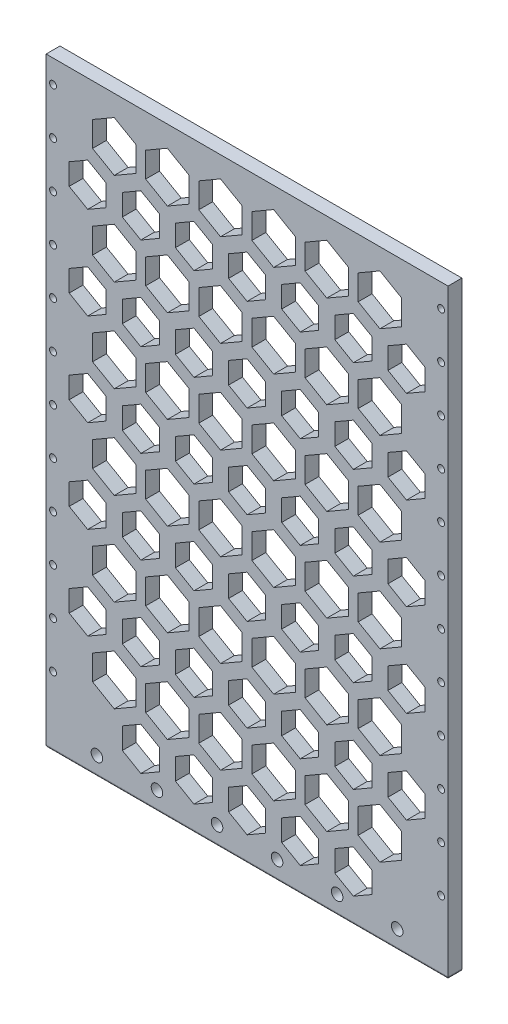
SolidWorks part; units mm, degrees
material "6061 Alloy"
ref_plane "前视基准面" through (0, 0, 0) normal (0, 0, 1) x (1, 0, 0)
ref_plane "上视基准面" through (0, 0, 0) normal (0, 1, 0) x (1, 0, 0)
ref_plane "右视基准面" through (0, 0, 0) normal (1, 0, 0) x (0, 0, -1)
sketch "Sketch1" plane through (0, 0, 0) normal (0, 0, 1) x (1, 0, 0)
  line L1 (-87, 90) -> (87, 90)
  line L2 (-87, 90) -> (-87, -150)
  line L3 (-87, -150) -> (87, -150)
  line L4 (87, 90) -> (87, -150)
  line L5 (-87, 90) -> (87, -150) construction
  line L6 (-87, -150) -> (87, 90) construction
  point P0 (0, -30)
  dimension "D1" = 174
  dimension "D2" = 240
extrude "Boss-Extrude1" add sketch "Sketch1" along normal blind 6
sketch "Sketch3" plane through (0, 0, 6) normal (0, 0, 1) x (1, 0, 0)
  line L6 (-77, -134) -> (77, -134) construction
  line L7 (-77, -134) -> (-77, -150) construction
  line L8 (-77, -150) -> (77, -150) construction
  line L9 (77, -134) -> (77, -150) construction
  line L10 (-77, -134) -> (77, -150) construction
  line L11 (-77, -150) -> (77, -134) construction
  circle A0 centre (-65, -142) radius 2.5
  circle A1 centre (-39, -142) radius 2.5
  circle A2 centre (-13, -142) radius 2.5
  circle A3 centre (13, -142) radius 2.5
  circle A4 centre (39, -142) radius 2.5
  circle A5 centre (65, -142) radius 2.5
  point P0 (0, -142)
  dimension "D1" = 12
  dimension "D2" = 6
extrude "Cut-Extrude1" cut sketch "Sketch3" against normal blind 6 contours A0 | A1 | A2 | A3 | A4 | A5
sketch "Sketch4" plane through (0, 90, 0) normal (0, 1, 0) x (1, 0, 0)
  line L4 (87, 0) -> (-87, 0)
  line L5 (-87, 0) -> (-87, -6)
  line L6 (-87, -6) -> (87, -6)
  line L7 (87, -6) -> (87, 0)
  line L8 (87, 0) -> (-87, 0)
  line L9 (-87, 0) -> (-87, -6)
  line L10 (-87, -6) -> (87, -6)
  line L11 (87, -6) -> (87, 0)
  dimension "D1" = 0
extrude "Boss-Extrude2" add sketch "Sketch4" along normal blind 20
sketch "Sketch6" plane through (0, 0, 6) normal (0, 0, 1) x (1, 0, 0)
  line L0 (-87, 110) -> (87, 110) construction
  line L2 (-87, 110) -> (-87, -150) construction
  line L3 (87, -150) -> (87, 110) construction
  circle A0 centre (-84, 100) radius 1.5
  circle A1 centre (-84, 80) radius 1.5
  circle A2 centre (-84, 60) radius 1.5
  circle A3 centre (-84, 40) radius 1.5
  circle A4 centre (-84, 20) radius 1.5
  circle A5 centre (-84, 0) radius 1.5
  circle A6 centre (-84, -20) radius 1.5
  circle A7 centre (-84, -40) radius 1.5
  circle A8 centre (-84, -60) radius 1.5
  circle A9 centre (-84, -80) radius 1.5
  circle A10 centre (-84, -100) radius 1.5
  circle A11 centre (-84, -120) radius 1.5
  circle A15 centre (84, 100) radius 1.5
  circle A16 centre (84, 80) radius 1.5
  circle A17 centre (84, 60) radius 1.5
  circle A18 centre (84, 40) radius 1.5
  circle A19 centre (84, 20) radius 1.5
  circle A20 centre (84, 0) radius 1.5
  circle A21 centre (84, -20) radius 1.5
  circle A22 centre (84, -40) radius 1.5
  circle A23 centre (84, -60) radius 1.5
  circle A24 centre (84, -80) radius 1.5
  circle A25 centre (84, -100) radius 1.5
  circle A26 centre (84, -120) radius 1.5
  circle A30 centre (-84, -160) radius 1.5 [skipped]
  circle A31 centre (-84, -180) radius 1.5 [skipped]
  circle A32 centre (84, -160) radius 1.5 [skipped]
  circle A33 centre (84, -180) radius 1.5 [skipped]
  circle A34 centre (-84, -140) radius 1.5 [skipped]
  circle A35 centre (84, -140) radius 1.5 [skipped]
  dimension "D3" = 15
  dimension "D5" = 3
  dimension "D1" = 10
  dimension "D2" = 3
  dimension "D4" = 3
  dimension "D6" = 10
  dimension "D7" = 15
extrude "Cut-Extrude2" cut sketch "Sketch6" against normal blind 10
sketch "Sketch7" plane through (0, 0, 6) normal (0, 0, 1) x (1, 0, 0)
  line L80 (-46, 60.7624) -> (-38, 65.3812)
  line L81 (-38, 65.3812) -> (-38, 74.6188)
  line L82 (-38, 74.6188) -> (-46, 79.2376)
  line L83 (-46, 79.2376) -> (-54, 74.6188)
  line L84 (-54, 74.6188) -> (-54, 65.3812)
  line L85 (-54, 65.3812) -> (-46, 60.7624)
  line L86 (-23, 60.7624) -> (-15, 65.3812)
  line L87 (-15, 65.3812) -> (-15, 74.6188)
  line L88 (-15, 74.6188) -> (-23, 79.2376)
  line L89 (-23, 79.2376) -> (-31, 74.6188)
  line L90 (-31, 74.6188) -> (-31, 65.3812)
  line L91 (-31, 65.3812) -> (-23, 60.7624)
  line L92 (0, 60.7624) -> (8, 65.3812)
  line L93 (8, 65.3812) -> (8, 74.6188)
  line L94 (8, 74.6188) -> (0, 79.2376)
  line L95 (0, 79.2376) -> (-8, 74.6188)
  line L96 (-8, 74.6188) -> (-8, 65.3812)
  line L97 (-8, 65.3812) -> (0, 60.7624)
  line L98 (23, 60.7624) -> (31, 65.3812)
  line L99 (31, 65.3812) -> (31, 74.6188)
  line L100 (31, 74.6188) -> (23, 79.2376)
  line L101 (23, 79.2376) -> (15, 74.6188)
  line L102 (15, 74.6188) -> (15, 65.3812)
  line L103 (15, 65.3812) -> (23, 60.7624)
  line L104 (46, 60.7624) -> (54, 65.3812)
  line L105 (54, 65.3812) -> (54, 74.6188)
  line L106 (54, 74.6188) -> (46, 79.2376)
  line L107 (46, 79.2376) -> (38, 74.6188)
  line L108 (38, 74.6188) -> (38, 65.3812)
  line L109 (38, 65.3812) -> (46, 60.7624)
  line L110 (69, 60.7624) -> (77, 65.3812)
  line L111 (77, 65.3812) -> (77, 74.6188)
  line L112 (77, 74.6188) -> (69, 79.2376)
  line L113 (69, 79.2376) -> (61, 74.6188)
  line L114 (61, 74.6188) -> (61, 65.3812)
  line L115 (61, 65.3812) -> (69, 60.7624)
  line L116 (-46, 20.7624) -> (-38, 25.3812)
  line L117 (-38, 25.3812) -> (-38, 34.6188)
  line L118 (-38, 34.6188) -> (-46, 39.2376)
  line L119 (-46, 39.2376) -> (-54, 34.6188)
  line L120 (-54, 34.6188) -> (-54, 25.3812)
  line L121 (-54, 25.3812) -> (-46, 20.7624)
  line L122 (-23, 20.7624) -> (-15, 25.3812)
  line L123 (-15, 25.3812) -> (-15, 34.6188)
  line L124 (-15, 34.6188) -> (-23, 39.2376)
  line L125 (-23, 39.2376) -> (-31, 34.6188)
  line L126 (-31, 34.6188) -> (-31, 25.3812)
  line L127 (-31, 25.3812) -> (-23, 20.7624)
  line L128 (0, 20.7624) -> (8, 25.3812)
  line L129 (8, 25.3812) -> (8, 34.6188)
  line L130 (8, 34.6188) -> (0, 39.2376)
  line L131 (0, 39.2376) -> (-8, 34.6188)
  line L132 (-8, 34.6188) -> (-8, 25.3812)
  line L133 (-8, 25.3812) -> (0, 20.7624)
  line L134 (23, 20.7624) -> (31, 25.3812)
  line L135 (31, 25.3812) -> (31, 34.6188)
  line L136 (31, 34.6188) -> (23, 39.2376)
  line L137 (23, 39.2376) -> (15, 34.6188)
  line L138 (15, 34.6188) -> (15, 25.3812)
  line L139 (15, 25.3812) -> (23, 20.7624)
  line L140 (46, 20.7624) -> (54, 25.3812)
  line L141 (54, 25.3812) -> (54, 34.6188)
  line L142 (54, 34.6188) -> (46, 39.2376)
  line L143 (46, 39.2376) -> (38, 34.6188)
  line L144 (38, 34.6188) -> (38, 25.3812)
  line L145 (38, 25.3812) -> (46, 20.7624)
  line L146 (69, 20.7624) -> (77, 25.3812)
  line L147 (77, 25.3812) -> (77, 34.6188)
  line L148 (77, 34.6188) -> (69, 39.2376)
  line L149 (69, 39.2376) -> (61, 34.6188)
  line L150 (61, 34.6188) -> (61, 25.3812)
  line L151 (61, 25.3812) -> (69, 20.7624)
  line L152 (-46, -19.2376) -> (-38, -14.6188)
  line L153 (-38, -14.6188) -> (-38, -5.3812)
  line L154 (-38, -5.3812) -> (-46, -0.7624)
  line L155 (-46, -0.7624) -> (-54, -5.3812)
  line L156 (-54, -5.3812) -> (-54, -14.6188)
  line L157 (-54, -14.6188) -> (-46, -19.2376)
  line L158 (-23, -19.2376) -> (-15, -14.6188)
  line L159 (-15, -14.6188) -> (-15, -5.3812)
  line L160 (-15, -5.3812) -> (-23, -0.7624)
  line L161 (-23, -0.7624) -> (-31, -5.3812)
  line L162 (-31, -5.3812) -> (-31, -14.6188)
  line L163 (-31, -14.6188) -> (-23, -19.2376)
  line L164 (0, -19.2376) -> (8, -14.6188)
  line L165 (8, -14.6188) -> (8, -5.3812)
  line L166 (8, -5.3812) -> (0, -0.7624)
  line L167 (0, -0.7624) -> (-8, -5.3812)
  line L168 (-8, -5.3812) -> (-8, -14.6188)
  line L169 (-8, -14.6188) -> (0, -19.2376)
  line L170 (23, -19.2376) -> (31, -14.6188)
  line L171 (31, -14.6188) -> (31, -5.3812)
  line L172 (31, -5.3812) -> (23, -0.7624)
  line L173 (23, -0.7624) -> (15, -5.3812)
  line L174 (15, -5.3812) -> (15, -14.6188)
  line L175 (15, -14.6188) -> (23, -19.2376)
  line L176 (46, -19.2376) -> (54, -14.6188)
  line L177 (54, -14.6188) -> (54, -5.3812)
  line L178 (54, -5.3812) -> (46, -0.7624)
  line L179 (46, -0.7624) -> (38, -5.3812)
  line L180 (38, -5.3812) -> (38, -14.6188)
  line L181 (38, -14.6188) -> (46, -19.2376)
  line L182 (69, -19.2376) -> (77, -14.6188)
  line L183 (77, -14.6188) -> (77, -5.3812)
  line L184 (77, -5.3812) -> (69, -0.7624)
  line L185 (69, -0.7624) -> (61, -5.3812)
  line L186 (61, -5.3812) -> (61, -14.6188)
  line L187 (61, -14.6188) -> (69, -19.2376)
  line L188 (-46, -59.2376) -> (-38, -54.6188)
  line L189 (-38, -54.6188) -> (-38, -45.3812)
  line L190 (-38, -45.3812) -> (-46, -40.7624)
  line L191 (-46, -40.7624) -> (-54, -45.3812)
  line L192 (-54, -45.3812) -> (-54, -54.6188)
  line L193 (-54, -54.6188) -> (-46, -59.2376)
  line L194 (-23, -59.2376) -> (-15, -54.6188)
  line L195 (-15, -54.6188) -> (-15, -45.3812)
  line L196 (-15, -45.3812) -> (-23, -40.7624)
  line L197 (-23, -40.7624) -> (-31, -45.3812)
  line L198 (-31, -45.3812) -> (-31, -54.6188)
  line L199 (-31, -54.6188) -> (-23, -59.2376)
  line L200 (0, -59.2376) -> (8, -54.6188)
  line L201 (8, -54.6188) -> (8, -45.3812)
  line L202 (8, -45.3812) -> (0, -40.7624)
  line L203 (0, -40.7624) -> (-8, -45.3812)
  line L204 (-8, -45.3812) -> (-8, -54.6188)
  line L205 (-8, -54.6188) -> (0, -59.2376)
  line L206 (23, -59.2376) -> (31, -54.6188)
  line L207 (31, -54.6188) -> (31, -45.3812)
  line L208 (31, -45.3812) -> (23, -40.7624)
  line L209 (23, -40.7624) -> (15, -45.3812)
  line L210 (15, -45.3812) -> (15, -54.6188)
  line L211 (15, -54.6188) -> (23, -59.2376)
  line L212 (46, -59.2376) -> (54, -54.6188)
  line L213 (54, -54.6188) -> (54, -45.3812)
  line L214 (54, -45.3812) -> (46, -40.7624)
  line L215 (46, -40.7624) -> (38, -45.3812)
  line L216 (38, -45.3812) -> (38, -54.6188)
  line L217 (38, -54.6188) -> (46, -59.2376)
  line L218 (69, -59.2376) -> (77, -54.6188)
  line L219 (77, -54.6188) -> (77, -45.3812)
  line L220 (77, -45.3812) -> (69, -40.7624)
  line L221 (69, -40.7624) -> (61, -45.3812)
  line L222 (61, -45.3812) -> (61, -54.6188)
  line L223 (61, -54.6188) -> (69, -59.2376)
  line L224 (-46, -99.2376) -> (-38, -94.6188)
  line L225 (-38, -94.6188) -> (-38, -85.3812)
  line L226 (-38, -85.3812) -> (-46, -80.7624)
  line L227 (-46, -80.7624) -> (-54, -85.3812)
  line L228 (-54, -85.3812) -> (-54, -94.6188)
  line L229 (-54, -94.6188) -> (-46, -99.2376)
  line L230 (-23, -99.2376) -> (-15, -94.6188)
  line L231 (-15, -94.6188) -> (-15, -85.3812)
  line L232 (-15, -85.3812) -> (-23, -80.7624)
  line L233 (-23, -80.7624) -> (-31, -85.3812)
  line L234 (-31, -85.3812) -> (-31, -94.6188)
  line L235 (-31, -94.6188) -> (-23, -99.2376)
  line L236 (0, -99.2376) -> (8, -94.6188)
  line L237 (8, -94.6188) -> (8, -85.3812)
  line L238 (8, -85.3812) -> (0, -80.7624)
  line L239 (0, -80.7624) -> (-8, -85.3812)
  line L240 (-8, -85.3812) -> (-8, -94.6188)
  line L241 (-8, -94.6188) -> (0, -99.2376)
  line L242 (23, -99.2376) -> (31, -94.6188)
  line L243 (31, -94.6188) -> (31, -85.3812)
  line L244 (31, -85.3812) -> (23, -80.7624)
  line L245 (23, -80.7624) -> (15, -85.3812)
  line L246 (15, -85.3812) -> (15, -94.6188)
  line L247 (15, -94.6188) -> (23, -99.2376)
  line L248 (46, -99.2376) -> (54, -94.6188)
  line L249 (54, -94.6188) -> (54, -85.3812)
  line L250 (54, -85.3812) -> (46, -80.7624)
  line L251 (46, -80.7624) -> (38, -85.3812)
  line L252 (38, -85.3812) -> (38, -94.6188)
  line L253 (38, -94.6188) -> (46, -99.2376)
  line L254 (69, -99.2376) -> (77, -94.6188)
  line L255 (77, -94.6188) -> (77, -85.3812)
  line L256 (77, -85.3812) -> (69, -80.7624)
  line L257 (69, -80.7624) -> (61, -85.3812)
  line L258 (61, -85.3812) -> (61, -94.6188)
  line L259 (61, -94.6188) -> (69, -99.2376)
  line L260 (-46, -139.2376) -> (-38, -134.6188)
  line L261 (-38, -134.6188) -> (-38, -125.3812)
  line L262 (-38, -125.3812) -> (-46, -120.7624)
  line L263 (-46, -120.7624) -> (-54, -125.3812)
  line L264 (-54, -125.3812) -> (-54, -134.6188)
  line L265 (-54, -134.6188) -> (-46, -139.2376)
  line L266 (-23, -139.2376) -> (-15, -134.6188)
  line L267 (-15, -134.6188) -> (-15, -125.3812)
  line L268 (-15, -125.3812) -> (-23, -120.7624)
  line L269 (-23, -120.7624) -> (-31, -125.3812)
  line L270 (-31, -125.3812) -> (-31, -134.6188)
  line L271 (-31, -134.6188) -> (-23, -139.2376)
  line L272 (0, -139.2376) -> (8, -134.6188)
  line L273 (8, -134.6188) -> (8, -125.3812)
  line L274 (8, -125.3812) -> (0, -120.7624)
  line L275 (0, -120.7624) -> (-8, -125.3812)
  line L276 (-8, -125.3812) -> (-8, -134.6188)
  line L277 (-8, -134.6188) -> (0, -139.2376)
  line L278 (23, -139.2376) -> (31, -134.6188)
  line L279 (31, -134.6188) -> (31, -125.3812)
  line L280 (31, -125.3812) -> (23, -120.7624)
  line L281 (23, -120.7624) -> (15, -125.3812)
  line L282 (15, -125.3812) -> (15, -134.6188)
  line L283 (15, -134.6188) -> (23, -139.2376)
  line L284 (46, -139.2376) -> (54, -134.6188)
  line L285 (54, -134.6188) -> (54, -125.3812)
  line L286 (54, -125.3812) -> (46, -120.7624)
  line L287 (46, -120.7624) -> (38, -125.3812)
  line L288 (38, -125.3812) -> (38, -134.6188)
  line L289 (38, -134.6188) -> (46, -139.2376)
  line L302 (-69, 60.7624) -> (-61, 65.3812)
  line L303 (-61, 65.3812) -> (-61, 74.6188)
  line L304 (-61, 74.6188) -> (-69, 79.2376)
  line L305 (-69, 79.2376) -> (-77, 74.6188)
  line L306 (-77, 74.6188) -> (-77, 65.3812)
  line L307 (-77, 65.3812) -> (-69, 60.7624)
  line L308 (-69, 20.7624) -> (-61, 25.3812)
  line L309 (-61, 25.3812) -> (-61, 34.6188)
  line L310 (-61, 34.6188) -> (-69, 39.2376)
  line L311 (-69, 39.2376) -> (-77, 34.6188)
  line L312 (-77, 34.6188) -> (-77, 25.3812)
  line L313 (-77, 25.3812) -> (-69, 20.7624)
  line L314 (-69, -19.2376) -> (-61, -14.6188)
  line L315 (-61, -14.6188) -> (-61, -5.3812)
  line L316 (-61, -5.3812) -> (-69, -0.7624)
  line L317 (-69, -0.7624) -> (-77, -5.3812)
  line L318 (-77, -5.3812) -> (-77, -14.6188)
  line L319 (-77, -14.6188) -> (-69, -19.2376)
  line L320 (-69, -59.2376) -> (-61, -54.6188)
  line L321 (-61, -54.6188) -> (-61, -45.3812)
  line L322 (-61, -45.3812) -> (-69, -40.7624)
  line L323 (-69, -40.7624) -> (-77, -45.3812)
  line L324 (-77, -45.3812) -> (-77, -54.6188)
  line L325 (-77, -54.6188) -> (-69, -59.2376)
  line L326 (-69, -99.2376) -> (-61, -94.6188)
  line L327 (-61, -94.6188) -> (-61, -85.3812)
  line L328 (-61, -85.3812) -> (-69, -80.7624)
  line L329 (-69, -80.7624) -> (-77, -85.3812)
  line L330 (-77, -85.3812) -> (-77, -94.6188)
  line L331 (-77, -94.6188) -> (-69, -99.2376)
  line L376 (-34.5, 79.2376) -> (-25.109, 84.6595)
  line L377 (-25.109, 84.6595) -> (-25.109, 95.5033)
  line L378 (-25.109, 95.5033) -> (-34.5, 100.9252)
  line L379 (-34.5, 100.9252) -> (-43.891, 95.5033)
  line L380 (-43.891, 95.5033) -> (-43.891, 84.6595)
  line L381 (-43.891, 84.6595) -> (-34.5, 79.2376)
  line L382 (-11.5, 79.2376) -> (-2.109, 84.6595)
  line L383 (-2.109, 84.6595) -> (-2.109, 95.5033)
  line L384 (-2.109, 95.5033) -> (-11.5, 100.9252)
  line L385 (-11.5, 100.9252) -> (-20.891, 95.5033)
  line L386 (-20.891, 95.5033) -> (-20.891, 84.6595)
  line L387 (-20.891, 84.6595) -> (-11.5, 79.2376)
  line L388 (11.5, 79.2376) -> (20.891, 84.6595)
  line L389 (20.891, 84.6595) -> (20.891, 95.5033)
  line L390 (20.891, 95.5033) -> (11.5, 100.9252)
  line L391 (11.5, 100.9252) -> (2.109, 95.5033)
  line L392 (2.109, 95.5033) -> (2.109, 84.6595)
  line L393 (2.109, 84.6595) -> (11.5, 79.2376)
  line L394 (34.5, 79.2376) -> (43.891, 84.6595)
  line L395 (43.891, 84.6595) -> (43.891, 95.5033)
  line L396 (43.891, 95.5033) -> (34.5, 100.9252)
  line L397 (34.5, 100.9252) -> (25.109, 95.5033)
  line L398 (25.109, 95.5033) -> (25.109, 84.6595)
  line L399 (25.109, 84.6595) -> (34.5, 79.2376)
  line L400 (57.5, 79.2376) -> (66.891, 84.6595)
  line L401 (66.891, 84.6595) -> (66.891, 95.5033)
  line L402 (66.891, 95.5033) -> (57.5, 100.9252)
  line L403 (57.5, 100.9252) -> (48.109, 95.5033)
  line L404 (48.109, 95.5033) -> (48.109, 84.6595)
  line L405 (48.109, 84.6595) -> (57.5, 79.2376)
  line L406 (-34.5, 39.2376) -> (-25.109, 44.6595)
  line L407 (-25.109, 44.6595) -> (-25.109, 55.5033)
  line L408 (-25.109, 55.5033) -> (-34.5, 60.9252)
  line L409 (-34.5, 60.9252) -> (-43.891, 55.5033)
  line L410 (-43.891, 55.5033) -> (-43.891, 44.6595)
  line L411 (-43.891, 44.6595) -> (-34.5, 39.2376)
  line L412 (-11.5, 39.2376) -> (-2.109, 44.6595)
  line L413 (-2.109, 44.6595) -> (-2.109, 55.5033)
  line L414 (-2.109, 55.5033) -> (-11.5, 60.9252)
  line L415 (-11.5, 60.9252) -> (-20.891, 55.5033)
  line L416 (-20.891, 55.5033) -> (-20.891, 44.6595)
  line L417 (-20.891, 44.6595) -> (-11.5, 39.2376)
  line L418 (11.5, 39.2376) -> (20.891, 44.6595)
  line L419 (20.891, 44.6595) -> (20.891, 55.5033)
  line L420 (20.891, 55.5033) -> (11.5, 60.9252)
  line L421 (11.5, 60.9252) -> (2.109, 55.5033)
  line L422 (2.109, 55.5033) -> (2.109, 44.6595)
  line L423 (2.109, 44.6595) -> (11.5, 39.2376)
  line L424 (34.5, 39.2376) -> (43.891, 44.6595)
  line L425 (43.891, 44.6595) -> (43.891, 55.5033)
  line L426 (43.891, 55.5033) -> (34.5, 60.9252)
  line L427 (34.5, 60.9252) -> (25.109, 55.5033)
  line L428 (25.109, 55.5033) -> (25.109, 44.6595)
  line L429 (25.109, 44.6595) -> (34.5, 39.2376)
  line L430 (57.5, 39.2376) -> (66.891, 44.6595)
  line L431 (66.891, 44.6595) -> (66.891, 55.5033)
  line L432 (66.891, 55.5033) -> (57.5, 60.9252)
  line L433 (57.5, 60.9252) -> (48.109, 55.5033)
  line L434 (48.109, 55.5033) -> (48.109, 44.6595)
  line L435 (48.109, 44.6595) -> (57.5, 39.2376)
  line L436 (-34.5, -0.7624) -> (-25.109, 4.6595)
  line L437 (-25.109, 4.6595) -> (-25.109, 15.5033)
  line L438 (-25.109, 15.5033) -> (-34.5, 20.9252)
  line L439 (-34.5, 20.9252) -> (-43.891, 15.5033)
  line L440 (-43.891, 15.5033) -> (-43.891, 4.6595)
  line L441 (-43.891, 4.6595) -> (-34.5, -0.7624)
  line L442 (-11.5, -0.7624) -> (-2.109, 4.6595)
  line L443 (-2.109, 4.6595) -> (-2.109, 15.5033)
  line L444 (-2.109, 15.5033) -> (-11.5, 20.9252)
  line L445 (-11.5, 20.9252) -> (-20.891, 15.5033)
  line L446 (-20.891, 15.5033) -> (-20.891, 4.6595)
  line L447 (-20.891, 4.6595) -> (-11.5, -0.7624)
  line L448 (11.5, -0.7624) -> (20.891, 4.6595)
  line L449 (20.891, 4.6595) -> (20.891, 15.5033)
  line L450 (20.891, 15.5033) -> (11.5, 20.9252)
  line L451 (11.5, 20.9252) -> (2.109, 15.5033)
  line L452 (2.109, 15.5033) -> (2.109, 4.6595)
  line L453 (2.109, 4.6595) -> (11.5, -0.7624)
  line L454 (34.5, -0.7624) -> (43.891, 4.6595)
  line L455 (43.891, 4.6595) -> (43.891, 15.5033)
  line L456 (43.891, 15.5033) -> (34.5, 20.9252)
  line L457 (34.5, 20.9252) -> (25.109, 15.5033)
  line L458 (25.109, 15.5033) -> (25.109, 4.6595)
  line L459 (25.109, 4.6595) -> (34.5, -0.7624)
  line L460 (57.5, -0.7624) -> (66.891, 4.6595)
  line L461 (66.891, 4.6595) -> (66.891, 15.5033)
  line L462 (66.891, 15.5033) -> (57.5, 20.9252)
  line L463 (57.5, 20.9252) -> (48.109, 15.5033)
  line L464 (48.109, 15.5033) -> (48.109, 4.6595)
  line L465 (48.109, 4.6595) -> (57.5, -0.7624)
  line L466 (-34.5, -40.7624) -> (-25.109, -35.3405)
  line L467 (-25.109, -35.3405) -> (-25.109, -24.4967)
  line L468 (-25.109, -24.4967) -> (-34.5, -19.0748)
  line L469 (-34.5, -19.0748) -> (-43.891, -24.4967)
  line L470 (-43.891, -24.4967) -> (-43.891, -35.3405)
  line L471 (-43.891, -35.3405) -> (-34.5, -40.7624)
  line L472 (-11.5, -40.7624) -> (-2.109, -35.3405)
  line L473 (-2.109, -35.3405) -> (-2.109, -24.4967)
  line L474 (-2.109, -24.4967) -> (-11.5, -19.0748)
  line L475 (-11.5, -19.0748) -> (-20.891, -24.4967)
  line L476 (-20.891, -24.4967) -> (-20.891, -35.3405)
  line L477 (-20.891, -35.3405) -> (-11.5, -40.7624)
  line L478 (11.5, -40.7624) -> (20.891, -35.3405)
  line L479 (20.891, -35.3405) -> (20.891, -24.4967)
  line L480 (20.891, -24.4967) -> (11.5, -19.0748)
  line L481 (11.5, -19.0748) -> (2.109, -24.4967)
  line L482 (2.109, -24.4967) -> (2.109, -35.3405)
  line L483 (2.109, -35.3405) -> (11.5, -40.7624)
  line L484 (34.5, -40.7624) -> (43.891, -35.3405)
  line L485 (43.891, -35.3405) -> (43.891, -24.4967)
  line L486 (43.891, -24.4967) -> (34.5, -19.0748)
  line L487 (34.5, -19.0748) -> (25.109, -24.4967)
  line L488 (25.109, -24.4967) -> (25.109, -35.3405)
  line L489 (25.109, -35.3405) -> (34.5, -40.7624)
  line L490 (57.5, -40.7624) -> (66.891, -35.3405)
  line L491 (66.891, -35.3405) -> (66.891, -24.4967)
  line L492 (66.891, -24.4967) -> (57.5, -19.0748)
  line L493 (57.5, -19.0748) -> (48.109, -24.4967)
  line L494 (48.109, -24.4967) -> (48.109, -35.3405)
  line L495 (48.109, -35.3405) -> (57.5, -40.7624)
  line L496 (-34.5, -80.7624) -> (-25.109, -75.3405)
  line L497 (-25.109, -75.3405) -> (-25.109, -64.4967)
  line L498 (-25.109, -64.4967) -> (-34.5, -59.0748)
  line L499 (-34.5, -59.0748) -> (-43.891, -64.4967)
  line L500 (-43.891, -64.4967) -> (-43.891, -75.3405)
  line L501 (-43.891, -75.3405) -> (-34.5, -80.7624)
  line L502 (-11.5, -80.7624) -> (-2.109, -75.3405)
  line L503 (-2.109, -75.3405) -> (-2.109, -64.4967)
  line L504 (-2.109, -64.4967) -> (-11.5, -59.0748)
  line L505 (-11.5, -59.0748) -> (-20.891, -64.4967)
  line L506 (-20.891, -64.4967) -> (-20.891, -75.3405)
  line L507 (-20.891, -75.3405) -> (-11.5, -80.7624)
  line L508 (11.5, -80.7624) -> (20.891, -75.3405)
  line L509 (20.891, -75.3405) -> (20.891, -64.4967)
  line L510 (20.891, -64.4967) -> (11.5, -59.0748)
  line L511 (11.5, -59.0748) -> (2.109, -64.4967)
  line L512 (2.109, -64.4967) -> (2.109, -75.3405)
  line L513 (2.109, -75.3405) -> (11.5, -80.7624)
  line L514 (34.5, -80.7624) -> (43.891, -75.3405)
  line L515 (43.891, -75.3405) -> (43.891, -64.4967)
  line L516 (43.891, -64.4967) -> (34.5, -59.0748)
  line L517 (34.5, -59.0748) -> (25.109, -64.4967)
  line L518 (25.109, -64.4967) -> (25.109, -75.3405)
  line L519 (25.109, -75.3405) -> (34.5, -80.7624)
  line L520 (57.5, -80.7624) -> (66.891, -75.3405)
  line L521 (66.891, -75.3405) -> (66.891, -64.4967)
  line L522 (66.891, -64.4967) -> (57.5, -59.0748)
  line L523 (57.5, -59.0748) -> (48.109, -64.4967)
  line L524 (48.109, -64.4967) -> (48.109, -75.3405)
  line L525 (48.109, -75.3405) -> (57.5, -80.7624)
  line L526 (-34.5, -120.7624) -> (-25.109, -115.3405)
  line L527 (-25.109, -115.3405) -> (-25.109, -104.4967)
  line L528 (-25.109, -104.4967) -> (-34.5, -99.0748)
  line L529 (-34.5, -99.0748) -> (-43.891, -104.4967)
  line L530 (-43.891, -104.4967) -> (-43.891, -115.3405)
  line L531 (-43.891, -115.3405) -> (-34.5, -120.7624)
  line L532 (-11.5, -120.7624) -> (-2.109, -115.3405)
  line L533 (-2.109, -115.3405) -> (-2.109, -104.4967)
  line L534 (-2.109, -104.4967) -> (-11.5, -99.0748)
  line L535 (-11.5, -99.0748) -> (-20.891, -104.4967)
  line L536 (-20.891, -104.4967) -> (-20.891, -115.3405)
  line L537 (-20.891, -115.3405) -> (-11.5, -120.7624)
  line L538 (11.5, -120.7624) -> (20.891, -115.3405)
  line L539 (20.891, -115.3405) -> (20.891, -104.4967)
  line L540 (20.891, -104.4967) -> (11.5, -99.0748)
  line L541 (11.5, -99.0748) -> (2.109, -104.4967)
  line L542 (2.109, -104.4967) -> (2.109, -115.3405)
  line L543 (2.109, -115.3405) -> (11.5, -120.7624)
  line L544 (34.5, -120.7624) -> (43.891, -115.3405)
  line L545 (43.891, -115.3405) -> (43.891, -104.4967)
  line L546 (43.891, -104.4967) -> (34.5, -99.0748)
  line L547 (34.5, -99.0748) -> (25.109, -104.4967)
  line L548 (25.109, -104.4967) -> (25.109, -115.3405)
  line L549 (25.109, -115.3405) -> (34.5, -120.7624)
  line L550 (57.5, -120.7624) -> (66.891, -115.3405)
  line L551 (66.891, -115.3405) -> (66.891, -104.4967)
  line L552 (66.891, -104.4967) -> (57.5, -99.0748)
  line L553 (57.5, -99.0748) -> (48.109, -104.4967)
  line L554 (48.109, -104.4967) -> (48.109, -115.3405)
  line L555 (48.109, -115.3405) -> (57.5, -120.7624)
  line L556 (-57.5, 79.2376) -> (-48.109, 84.6595)
  line L557 (-48.109, 84.6595) -> (-48.109, 95.5033)
  line L558 (-48.109, 95.5033) -> (-57.5, 100.9252)
  line L559 (-57.5, 100.9252) -> (-66.891, 95.5033)
  line L560 (-66.891, 95.5033) -> (-66.891, 84.6595)
  line L561 (-66.891, 84.6595) -> (-57.5, 79.2376)
  line L562 (-57.5, 39.2376) -> (-48.109, 44.6595)
  line L563 (-48.109, 44.6595) -> (-48.109, 55.5033)
  line L564 (-48.109, 55.5033) -> (-57.5, 60.9252)
  line L565 (-57.5, 60.9252) -> (-66.891, 55.5033)
  line L566 (-66.891, 55.5033) -> (-66.891, 44.6595)
  line L567 (-66.891, 44.6595) -> (-57.5, 39.2376)
  line L568 (-57.5, -0.7624) -> (-48.109, 4.6595)
  line L569 (-48.109, 4.6595) -> (-48.109, 15.5033)
  line L570 (-48.109, 15.5033) -> (-57.5, 20.9252)
  line L571 (-57.5, 20.9252) -> (-66.891, 15.5033)
  line L572 (-66.891, 15.5033) -> (-66.891, 4.6595)
  line L573 (-66.891, 4.6595) -> (-57.5, -0.7624)
  line L574 (-57.5, -40.7624) -> (-48.109, -35.3405)
  line L575 (-48.109, -35.3405) -> (-48.109, -24.4967)
  line L576 (-48.109, -24.4967) -> (-57.5, -19.0748)
  line L577 (-57.5, -19.0748) -> (-66.891, -24.4967)
  line L578 (-66.891, -24.4967) -> (-66.891, -35.3405)
  line L579 (-66.891, -35.3405) -> (-57.5, -40.7624)
  line L580 (-57.5, -80.7624) -> (-48.109, -75.3405)
  line L581 (-48.109, -75.3405) -> (-48.109, -64.4967)
  line L582 (-48.109, -64.4967) -> (-57.5, -59.0748)
  line L583 (-57.5, -59.0748) -> (-66.891, -64.4967)
  line L584 (-66.891, -64.4967) -> (-66.891, -75.3405)
  line L585 (-66.891, -75.3405) -> (-57.5, -80.7624)
  line L586 (-57.5, -120.7624) -> (-48.109, -115.3405)
  line L587 (-48.109, -115.3405) -> (-48.109, -104.4967)
  line L588 (-48.109, -104.4967) -> (-57.5, -99.0748)
  line L589 (-57.5, -99.0748) -> (-66.891, -104.4967)
  line L590 (-66.891, -104.4967) -> (-66.891, -115.3405)
  line L591 (-66.891, -115.3405) -> (-57.5, -120.7624)
  circle A13 centre (-46, 70) radius 8 construction
  circle A14 centre (-23, 70) radius 8 construction
  circle A15 centre (0, 70) radius 8 construction
  circle A16 centre (23, 70) radius 8 construction
  circle A17 centre (46, 70) radius 8 construction
  circle A18 centre (69, 70) radius 8 construction
  circle A19 centre (-46, 30) radius 8 construction
  circle A20 centre (-23, 30) radius 8 construction
  circle A21 centre (0, 30) radius 8 construction
  circle A22 centre (23, 30) radius 8 construction
  circle A23 centre (46, 30) radius 8 construction
  circle A24 centre (69, 30) radius 8 construction
  circle A25 centre (-46, -10) radius 8 construction
  circle A26 centre (-23, -10) radius 8 construction
  circle A27 centre (0, -10) radius 8 construction
  circle A28 centre (23, -10) radius 8 construction
  circle A29 centre (46, -10) radius 8 construction
  circle A30 centre (69, -10) radius 8 construction
  circle A31 centre (-46, -50) radius 8 construction
  circle A32 centre (-23, -50) radius 8 construction
  circle A33 centre (0, -50) radius 8 construction
  circle A34 centre (23, -50) radius 8 construction
  circle A35 centre (46, -50) radius 8 construction
  circle A36 centre (69, -50) radius 8 construction
  circle A37 centre (-46, -90) radius 8 construction
  circle A38 centre (-23, -90) radius 8 construction
  circle A39 centre (0, -90) radius 8 construction
  circle A40 centre (23, -90) radius 8 construction
  circle A41 centre (46, -90) radius 8 construction
  circle A42 centre (69, -90) radius 8 construction
  circle A43 centre (-46, -130) radius 8 construction
  circle A44 centre (-23, -130) radius 8 construction
  circle A45 centre (0, -130) radius 8 construction
  circle A46 centre (23, -130) radius 8 construction
  circle A47 centre (46, -130) radius 8 construction
  circle A50 centre (-69, 70) radius 8 construction
  circle A51 centre (-69, 30) radius 8 construction
  circle A52 centre (-69, -10) radius 8 construction
  circle A53 centre (-69, -50) radius 8 construction
  circle A54 centre (-69, -90) radius 8 construction
extrude "Cut-Extrude3" cut sketch "Sketch7" against normal blind 10
fillet "Fillet2" radius 1 3 edges at (0, -150, 6) (-87, -150, 3) (87, -150, 3)
